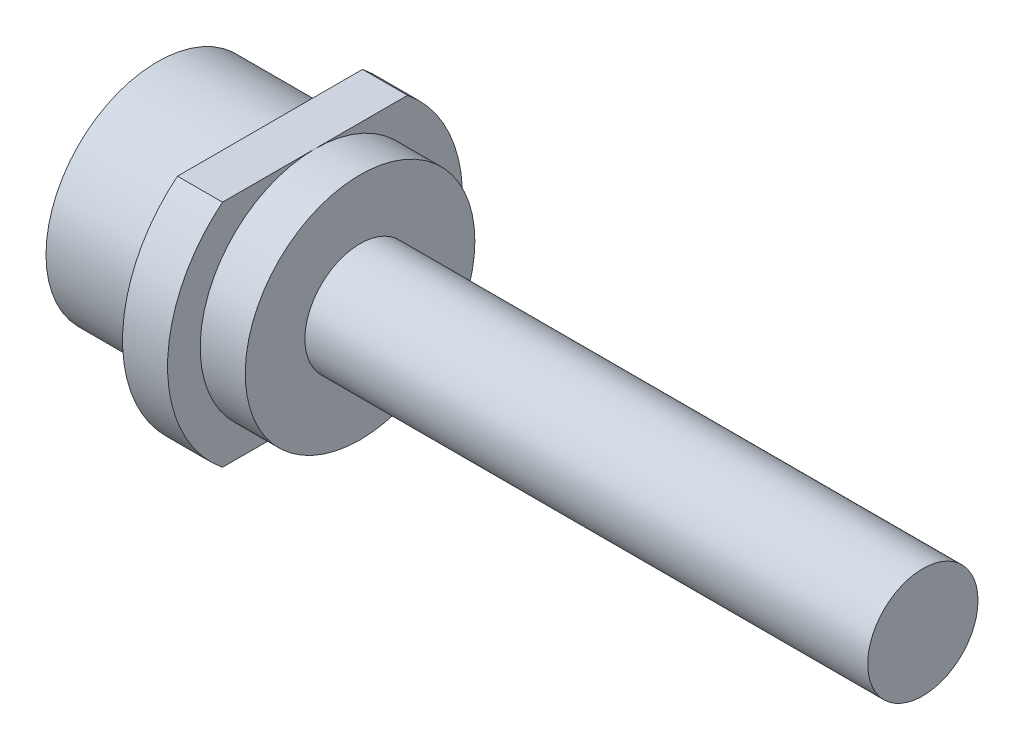
SolidWorks part; units mm, degrees
ref_plane "前视基准面" through (0, 0, 0) normal (0, 0, 1) x (1, 0, 0)
ref_plane "上视基准面" through (0, 0, 0) normal (0, 1, 0) x (1, 0, 0)
ref_plane "右视基准面" through (0, 0, 0) normal (1, 0, 0) x (0, 0, -1)
sketch "草图2" plane through (0, 0, 0) normal (1, 0, 0) x (0, 0, -1)
  line L0 (4.11, 5.1) -> (-4.11, 5.1)
  line L1 (4.11, -5.1) -> (-4.11, -5.1)
  arc A0 (-4.11, 5.1) -> (-4.11, -5.1) centre (0, 0) ccw
  arc A1 (4.11, -5.1) -> (4.11, 5.1) centre (0, 0) ccw
  dimension "D1" = 13.1
  dimension "D2" = 10.2
  dimension "D3" = 5.1
extrude "凸台-拉伸1" add sketch "草图2" along normal blind 2
sketch "草图3" plane through (2, 0, 0) normal (1, 0, 0) x (0, 0, -1)
  circle A0 centre (0, 0) radius 5.1
extrude "凸台-拉伸2" add sketch "草图3" along normal blind 2
sketch "草图4" plane through (4, 0, 0) normal (1, 0, 0) x (0, 0, -1)
  circle A0 centre (0, 0) radius 2.45
  dimension "D1" = 4.9
extrude "凸台-拉伸3" add sketch "草图4" along normal blind 25
sketch "草图5" plane through (0, 0, 0) normal (-1, 0, 0) x (0, 0, 1)
  circle A0 centre (0, 0) radius 4.95
extrude "凸台-拉伸4" add sketch "草图5" along normal blind 5
